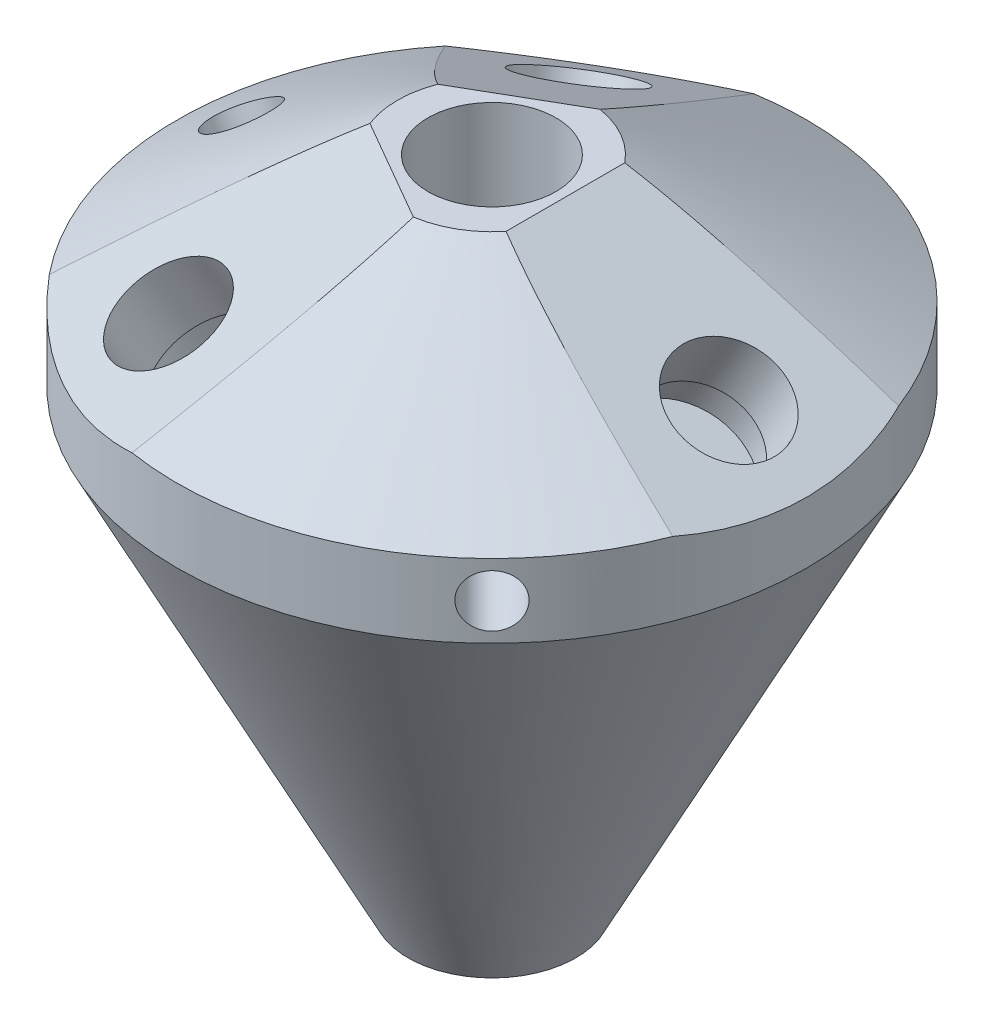
SolidWorks part; units mm, degrees
ref_plane "正面" through (0, 0, 0) normal (0, 0, 1) x (1, 0, 0)
ref_plane "平面" through (0, 0, 0) normal (0, 1, 0) x (1, 0, 0)
ref_plane "右側面" through (0, 0, 0) normal (1, 0, 0) x (0, 0, -1)
sketch "ｽｹｯﾁ1" plane through (0, 0, 0) normal (0, 0, 1) x (1, 0, 0)
  line L0 (0, -31.1509) -> (0, 0)
  line L1 (0, 0) -> (-4.5, 0)
  line L2 (-4.5, 0) -> (-15, -6.0622)
  line L3 (-15, -6.0622) -> (-15, -9.5622)
  line L4 (-15, -9.5622) -> (-4, -31.1509)
  line L5 (-4, -31.1509) -> (0, -31.1509)
  dimension "D1" = 4.5
  dimension "D2" = 15
  dimension "D3" = 93
  dimension "D4" = 30
  dimension "D5" = 4
  dimension "D6" = 3.5
revolve "回転1" add sketch "ｽｹｯﾁ1" angle 360 about L0
hole_wizard "M6 すきま穴1" positions "ｽｹｯﾁ11" profile "ｽｹｯﾁ12" hole size "M6" standard "ISO"
sketch "ｽｹｯﾁ11" plane through (0, 0, 0) normal (0, 1, 0) x (1, 0, 0)
  point P0 (0, 0)
sketch "ｽｹｯﾁ12" plane through (0, 0, 0) normal (1, 0, 0) x (0, 0, 1)
  line L0 (0, 0) -> (0, 16.8326)
  line L1 (0, 16.8326) -> (3.05, 15)
  line L2 (3.05, 15) -> (3.05, 0)
  line L5 (3.05, 0) -> (0, 0)
  line L10 (0, 16.8326) -> (-3.05, 15) construction
  line L11 (0, -6.35) -> (0, 107.95) construction
  dimension "穴の直径" = 6.1
  dimension "穴の深さ" = 15
  dimension "ﾄﾞﾘﾙ角度" = 118
sketch "ｽｹｯﾁ13" plane through (0, 0, 0) normal (0, 0, 1) x (1, 0, 0)
  line L0 (0.1, -23.8697) -> (15.0754, 2.0684)
  line L1 (-4, -31.1509) -> (4, -31.1509) construction
  line L2 (-4, -31.1509) -> (4, -31.1509)
  line L3 (0, 0) -> (0, -31.1509)
  line L4 (15, -6.0622) -> (-15, -6.0622) construction
  line L5 (15, -6.0622) -> (-15, -6.0622)
  line L6 (0.1, -23.8697) -> (0, -24.0429) construction
  dimension "D1" = 30
  dimension "D2" = 4
  dimension "D3" = 0.1
sweep "ｶｯﾄ - ｽｲｰﾌﾟ1" cut path "ｽｹｯﾁ13" circular profile diameter 2 parameters "D3"=2
ref_plane "平面2" through (1.125, 1.9486, 0) normal (0.5, 0.866, 0) x (0.866, -0.5, 0)
ref_plane "平面6" through (0.875, 1.5155, 0) normal (0.5, 0.866, 0) x (0.866, -0.5, 0)
sketch "ｽｹｯﾁ66" plane through (0.875, 1.5155, 0) normal (0.5, 0.866, 0) x (0.866, -0.5, 0)
  line L1 (37.049, -21.7599) -> (-13.0061, -21.7599)
  line L2 (37.049, -21.7599) -> (37.049, 21.7599)
  line L3 (37.049, 21.7599) -> (-13.0061, 21.7599)
  line L4 (-13.0061, -21.7599) -> (-13.0061, 21.7599)
  line L5 (37.049, -21.7599) -> (-13.0061, 21.7599) construction
  line L6 (37.049, 21.7599) -> (-13.0061, -21.7599) construction
  point P0 (12.0215, 0)
extrude "ｶｯﾄ - 押し出し4" cut sketch "ｽｹｯﾁ66" along normal blind 10
sketch "ｽｹｯﾁ65" plane through (1.125, 1.9486, 0) normal (0.5, 0.866, 0) x (0.866, -0.5, 0)
  line L1 (37.7036, -5) -> (-13.6607, -5)
  line L2 (37.7036, -5) -> (37.7036, 5)
  line L3 (37.7036, 5) -> (-13.6607, 5)
  line L4 (-13.6607, -5) -> (-13.6607, 5)
  line L5 (37.7036, -5) -> (-13.6607, 5) construction
  line L6 (37.7036, 5) -> (-13.6607, -5) construction
  point P0 (12.0215, 0)
  dimension "D1" = 10
sketch "ｽｹｯﾁ25" plane through (0.875, 1.5155, 0) normal (0.5, 0.866, 0) x (0.866, -0.5, 0)
  circle A2 centre (12.0215, 0) radius 1 construction
  circle A3 centre (12.0215, 0) radius 1
  point P0 (12.0215, 0)
hole_wizard "M6 ねじ穴2" positions "ｽｹｯﾁ25" profile "ｽｹｯﾁ26" tap size "M6" standard "ISO"
sketch "ｽｹｯﾁ26" plane through (11.2859, -4.4952, 0) normal (0, 0, 1) x (-0.866, 0.5, 0)
  line L0 (0, 0) -> (0, 5)
  line L1 (0, 5) -> (2.5, 5)
  line L2 (2.5, 5) -> (2.5, 0)
  line L5 (2.5, 0) -> (0, 0)
  line L10 (0, 5) -> (-2.5, 5) construction
  line L11 (0, -6.35) -> (0, 107.95) construction
  dimension "ねじ下穴ﾄﾞﾘﾙ直径" = 5
  dimension "ねじ下穴ﾄﾞﾘﾙの深さ" = 5
  dimension "ﾄﾞﾘﾙ角度" = 180
cosmetic thread "穴のねじ山13" parameters "D1"=12, "D2"=6
pattern_circular "円形ﾊﾟﾀｰﾝ3" count 3 over 360 about axis through (0, 0, 0) along (0, 1, 0) of "M6 ねじ穴2", "ｶｯﾄ - ｽｲｰﾌﾟ1", "ｶｯﾄ - 押し出し4"
cosmetic thread "穴のねじ山14" parameters "D1"=12, "D2"=6
cosmetic thread "穴のねじ山15" parameters "D1"=12, "D2"=6
sketch "ｽｹｯﾁ33" plane through (0, -31.1509, 0) normal (0, -1, 0) x (1, 0, 0)
  circle A0 centre (0, 0) radius 1
  dimension "D1" = 2
extrude "ｶｯﾄ - 押し出し3" cut sketch "ｽｹｯﾁ33" against normal blind 8
sketch "ｽｹｯﾁ46" plane through (0, -31.1509, 0) normal (0, -1, 0) x (1, 0, 0)
  circle A1 centre (0, 0) radius 4
  circle A2 centre (0, 0) radius 4
  point P2 (0, 0)
  dimension "D1" = 0
hole_wizard "M6 ねじ穴3" positions "ｽｹｯﾁ46" profile "ｽｹｯﾁ47" tap size "M6" standard "ISO"
sketch "ｽｹｯﾁ47" plane through (0, -31.1509, 0) normal (1, 0, 0) x (0, 0, -1)
  line L0 (0, 0) -> (0, 6)
  line L1 (0, 6) -> (2.5, 6)
  line L2 (2.5, 6) -> (2.5, 0)
  line L5 (2.5, 0) -> (0, 0)
  line L10 (0, 6) -> (-2.5, 6) construction
  line L11 (0, -6.35) -> (0, 107.95) construction
  dimension "ねじ下穴ﾄﾞﾘﾙ直径" = 5
  dimension "ねじ下穴ﾄﾞﾘﾙの深さ" = 6
  dimension "ﾄﾞﾘﾙ角度" = 180
cosmetic thread "穴のねじ山16" parameters "D1"=12, "D2"=6
sketch "ｽｹｯﾁ59" plane through (0, 0, 0) normal (0, 1, 0) x (1, 0, 0)
  point P0 (-8, 0)
  dimension "D1" = 8
hole_wizard "M6 すきま穴2" positions "ｽｹｯﾁ59" profile "ｽｹｯﾁ60" hole size "M6" standard "ISO"
sketch "ｽｹｯﾁ60" plane through (-8, 0, 0) normal (1, 0, 0) x (0, 0, 1)
  line L0 (0, 0) -> (0, 18.9313)
  line L1 (0, 18.9313) -> (1.55, 18)
  line L2 (1.55, 18) -> (1.55, 0)
  line L5 (1.55, 0) -> (0, 0)
  line L10 (0, 18.9313) -> (-1.55, 18) construction
  line L11 (0, -6.35) -> (0, 107.95) construction
  dimension "穴の直径" = 3.1
  dimension "穴の深さ" = 18
  dimension "ﾄﾞﾘﾙ角度" = 118
ref_plane "平面4" through (-15, 0, 0) normal (-1, 0, 0) x (0, 0, 1)
sketch "ｽｹｯﾁ61" plane through (-15, 0, 0) normal (-1, 0, 0) x (0, 0, 1)
  line L0 (-15, -6.0622) -> (15, -6.0622) construction
  line L1 (-15, -6.0622) -> (15, -6.0622)
  line L2 (-15, -9.5622) -> (15, -9.5622) construction
  line L3 (-15, -9.5622) -> (15, -9.5622)
  point P0 (0, -7.8122)
  dimension "D1" = 1.75
hole_wizard "M3 ねじ穴1" positions "ｽｹｯﾁ61" profile "ｽｹｯﾁ62" tap size "M3" standard "ISO"
sketch "ｽｹｯﾁ62" plane through (-15, -7.8122, 0) normal (0, 1, 0) x (0, 0, 1)
  line L0 (0, 0) -> (0, 5.7511)
  line L1 (0, 5.7511) -> (1.25, 5)
  line L2 (1.25, 5) -> (1.25, 0)
  line L5 (1.25, 0) -> (0, 0)
  line L10 (0, 5.7511) -> (-1.25, 5) construction
  line L11 (0, -6.35) -> (0, 107.95) construction
  dimension "ねじ下穴ﾄﾞﾘﾙ直径" = 2.5
  dimension "ねじ下穴ﾄﾞﾘﾙの深さ" = 5
  dimension "ﾄﾞﾘﾙ角度" = 118
cosmetic thread "穴のねじ山17" parameters "D1"=6, "D2"=3
ref_plane "平面5" through (10.6066, 0, 10.6066) normal (0.7071, 0, 0.7071) x (0, -1, 0)
sketch "ｽｹｯﾁ63" plane through (10.6066, 0, 10.6066) normal (0.7071, 0, 0.7071) x (0, -1, 0)
  line L0 (6.0622, 15) -> (6.0622, -15) construction
  point P0 (7.8122, 0)
  dimension "D1" = 1.75
hole_wizard "M3 ねじ穴2" positions "ｽｹｯﾁ63" profile "ｽｹｯﾁ64" tap size "M3" standard "ISO"
sketch "ｽｹｯﾁ64" plane through (10.6066, -7.8122, 10.6066) normal (0, 1, 0) x (0.7071, 0, -0.7071)
  line L0 (0, 0) -> (0, 15.7511)
  line L1 (0, 15.7511) -> (1.25, 15)
  line L2 (1.25, 15) -> (1.25, 0)
  line L5 (1.25, 0) -> (0, 0)
  line L10 (0, 15.7511) -> (-1.25, 15) construction
  line L11 (0, -6.35) -> (0, 107.95) construction
  dimension "ねじ下穴ﾄﾞﾘﾙ直径" = 2.5
  dimension "ねじ下穴ﾄﾞﾘﾙの深さ" = 15
  dimension "ﾄﾞﾘﾙ角度" = 118
cosmetic thread "穴のねじ山18" parameters "D1"=6, "D2"=3
ref_plane "平面10" through (0, 0, 0) normal (0, 0, -1) x (-1, 0, 0)
ref_plane "平面11" through (-1.125, 1.9486, 0) normal (-0.5, 0.866, 0) x (0.866, 0.5, 0)
sketch "ｽｹｯﾁ81" plane through (-1.125, 1.9486, 0) normal (-0.5, 0.866, 0) x (0.866, 0.5, 0)
  circle A0 centre (-12.5, 0) radius 1.55
  point P0 (-12.5, 0)
  dimension "D2" = 3.1
  dimension "D1" = 12.5
hole_wizard "M6 すきま穴3" positions "ｽｹｯﾁ82" profile "ｽｹｯﾁ83" hole size "M6" standard "ISO"
sketch "ｽｹｯﾁ82" plane through (-1.125, 1.9486, 0) normal (-0.5, 0.866, 0) x (0.866, 0.5, 0)
  point P0 (-12.5, 0)
sketch "ｽｹｯﾁ83" plane through (-11.9503, -4.3014, 0) normal (0, 0, 1) x (-0.866, -0.5, 0)
  line L0 (0, 0) -> (0, 15.9313)
  line L1 (0, 15.9313) -> (1.55, 15)
  line L2 (1.55, 15) -> (1.55, 0)
  line L5 (1.55, 0) -> (0, 0)
  line L10 (0, 15.9313) -> (-1.55, 15) construction
  line L11 (0, -6.35) -> (0, 107.95) construction
  dimension "穴の直径" = 3.1
  dimension "穴の深さ" = 15
  dimension "ﾄﾞﾘﾙ角度" = 118
sketch "ｽｹｯﾁ90" plane through (-1.625, -2.8146, 0) normal (0.5, 0.866, 0) x (0.866, -0.5, 0)
  circle A0 centre (12.0215, 0) radius 3
  circle A1 centre (12.0215, 0) radius 2.5
  circle A2 centre (12.0215, 0) radius 2.5
  circle M2 centre (12.0215, 0) radius 2.5
  circle M3 centre (12.0215, 0) radius 1
  dimension "D2" = 6
  dimension "D1" = 0
extrude "ｶｯﾄ - 押し出し5" cut sketch "ｽｹｯﾁ90" along normal blind 2 contours M2 M3 | A0 M2
pattern_circular "円形ﾊﾟﾀｰﾝ5" count 3 over 360 about axis through (0, 0, 0) along (0, 1, 0) of "ｶｯﾄ - 押し出し5"
sketch "ｽｹｯﾁ91" plane through (0, -25.1509, 0) normal (0, -1, 0) x (1, 0, 0)
  circle A0 centre (0, 0) radius 3
  circle A1 centre (0, 0) radius 2.5
  circle A2 centre (0, 0) radius 2.5
  circle M2 centre (0, 0) radius 2.5
  circle M3 centre (0, 0) radius 1
  dimension "D2" = 6
  dimension "D1" = 0
extrude "ｶｯﾄ - 押し出し6" cut sketch "ｽｹｯﾁ91" along normal blind 2 contours M2 M3 | A0 M2
